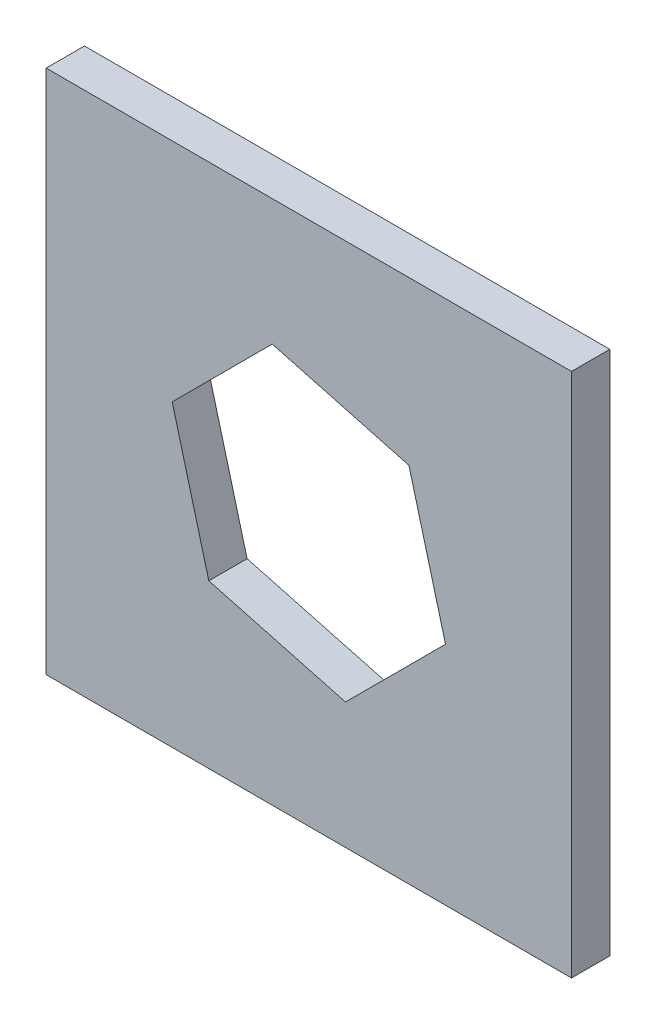
SolidWorks part; units mm, degrees
ref_plane "前视基准面" through (0, 0, 0) normal (0, 0, 1) x (1, 0, 0)
ref_plane "上视基准面" through (0, 0, 0) normal (0, 1, 0) x (1, 0, 0)
ref_plane "右视基准面" through (0, 0, 0) normal (1, 0, 0) x (0, 0, -1)
sketch "草图1" plane through (0, 0, 0) normal (0, 0, 1) x (1, 0, 0)
  line L1 (17.15, -17.15) -> (-17.15, -17.15)
  line L2 (17.15, -17.15) -> (17.15, 17.15)
  line L3 (17.15, 17.15) -> (-17.15, 17.15)
  line L4 (-17.15, -17.15) -> (-17.15, 17.15)
  line L5 (17.15, -17.15) -> (-17.15, 17.15) construction
  line L6 (17.15, 17.15) -> (-17.15, -17.15) construction
  line L7 (6.532, 6.532) -> (-2.3909, 8.9228)
  line L8 (-2.3909, 8.9228) -> (-8.9228, 2.3909)
  line L9 (-8.9228, 2.3909) -> (-6.532, -6.532)
  line L10 (-6.532, -6.532) -> (2.3909, -8.9228)
  line L11 (2.3909, -8.9228) -> (8.9228, -2.3909)
  line L12 (8.9228, -2.3909) -> (6.532, 6.532)
  circle A0 centre (0, 0) radius 8 construction
  point P0 (0, 0)
  dimension "D1" = 34.3
  dimension "D2" = 34.3
  dimension "D3" = 8
extrude "凸台-拉伸1" add sketch "草图1" along normal blind 2.5
